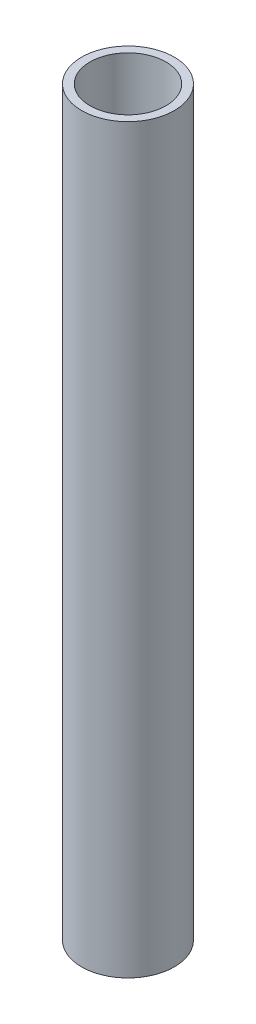
SolidWorks part; units mm, degrees
ref_plane "Front Plane" through (0, 0, 0) normal (0, 0, 1) x (1, 0, 0)
ref_plane "Top Plane" through (0, 0, 0) normal (0, 1, 0) x (1, 0, 0)
ref_plane "Right Plane" through (0, 0, 0) normal (1, 0, 0) x (0, 0, -1)
sketch "Sketch1" plane through (0, 0, 0) normal (0, 1, 0) x (1, 0, 0)
  circle A0 centre (0, 0) radius 12.7
  circle A1 centre (0, 0) radius 10.414
  dimension "D1" = 25.4
  dimension "D2" = 20.828
extrude "Boss-Extrude1" add sketch "Sketch1" along normal blind 203.2
